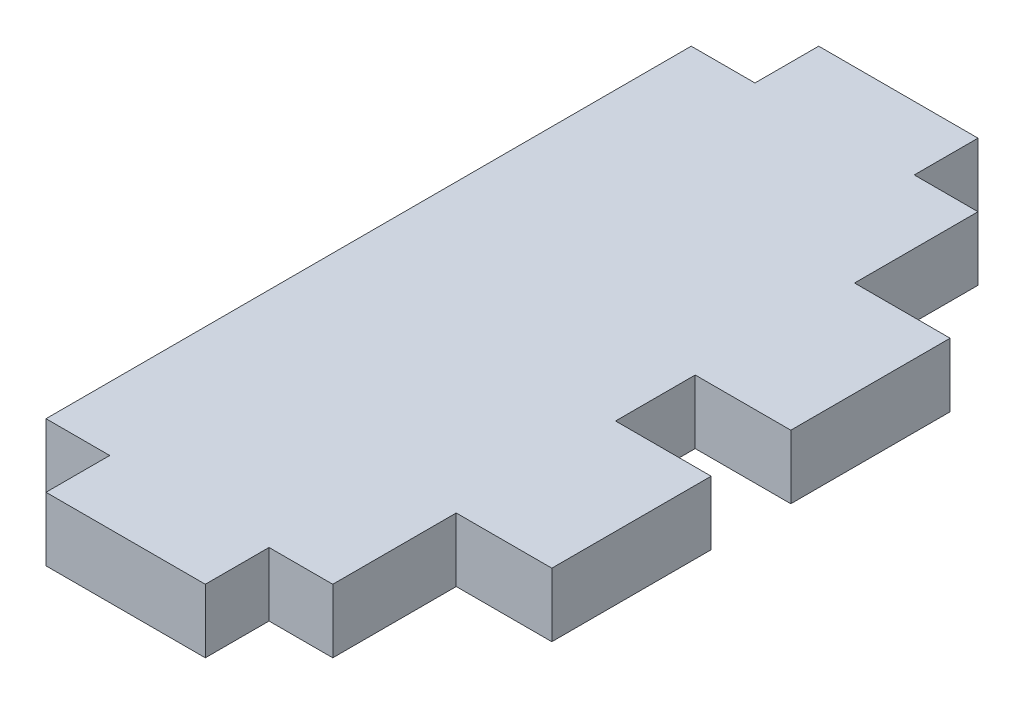
SolidWorks part; units mm, degrees
material "Maple"
ref_plane "Front Plane" through (0, 0, 0) normal (0, 0, 1) x (1, 0, 0)
ref_plane "Top Plane" through (0, 0, 0) normal (0, 1, 0) x (1, 0, 0)
ref_plane "Right Plane" through (0, 0, 0) normal (1, 0, 0) x (0, 0, -1)
sketch "Sketch1" plane through (0, 0, 0) normal (0, 1, 0) x (1, 0, 0)
  line L1 (0, 0) -> (18, 0)
  line L2 (0, 0) -> (0, -40.5)
  line L3 (0, -40.5) -> (18, -40.5)
  line L4 (18, 0) -> (18, -40.5)
  dimension "D1" = 18
  dimension "D2" = 40.5
extrude "Boss-Extrude1" add sketch "Sketch1" along normal blind 4
sketch "Sketch2" plane through (0, 0, 0) normal (0, -1, 0) x (-1, 0, 0)
  line L1 (-14, 0) -> (-4, 0)
  line L2 (-14, 0) -> (-14, 4)
  line L3 (-14, 4) -> (-4, 4)
  line L4 (-4, 0) -> (-4, 4)
  line L5 (-18, 0) -> (0, 0) construction
  line L6 (-14, -40.5) -> (-4, -40.5)
  line L7 (-14, -40.5) -> (-14, -44.5)
  line L8 (-14, -44.5) -> (-4, -44.5)
  line L9 (-4, -40.5) -> (-4, -44.5)
  line L10 (0, -40.5) -> (-18, -40.5) construction
  line L11 (-18, -40.5) -> (-18, 0) construction
  point P4 (-24.6884, 0)
  point P5 (-24.8346, 0)
  point P14 (0, 0)
  point P15 (0, 0)
  dimension "D1" = 10
  dimension "D2" = 4
  dimension "D3" = 10
  dimension "D4" = 4
  dimension "D5" = 4
extrude "Boss-Extrude2" add sketch "Sketch2" against normal through all
sketch "Sketch3" plane through (18, 0, 0) normal (1, 0, 0) x (0, 0, -1)
  line L5 (-40.5, 0) -> (0, 0) construction
  line L6 (-40.5, 4) -> (0, 4) construction
  line L8 (-17.75, 0) -> (-7.75, 0)
  line L9 (-17.75, 0) -> (-17.75, 4)
  line L10 (-17.75, 4) -> (-7.75, 4)
  line L11 (-7.75, 0) -> (-7.75, 4)
  line L12 (-22.75, 4) -> (-32.75, 4)
  line L13 (-22.75, 4) -> (-22.75, 0)
  line L14 (-22.75, 0) -> (-32.75, 0)
  line L15 (-32.75, 4) -> (-32.75, 0)
  line L20 (-20.25, 4) -> (-20.25, 0) construction
  line L21 (-40.5, 4) -> (0, 4) construction
  line L22 (-40.5, 0) -> (0, 0) construction
  point P4 (0, 0)
  point P30 (0, 0)
  dimension "D1" = 2.5
  dimension "D2" = 2.5
  dimension "D5" = 10
  dimension "D6" = 10
extrude "Boss-Extrude3" add sketch "Sketch3" along normal blind 6
equation "\"D3@Sketch2\"=\"D1@Sketch2\""
equation "\"D4@Sketch2\"=\"D2@Sketch2\""
